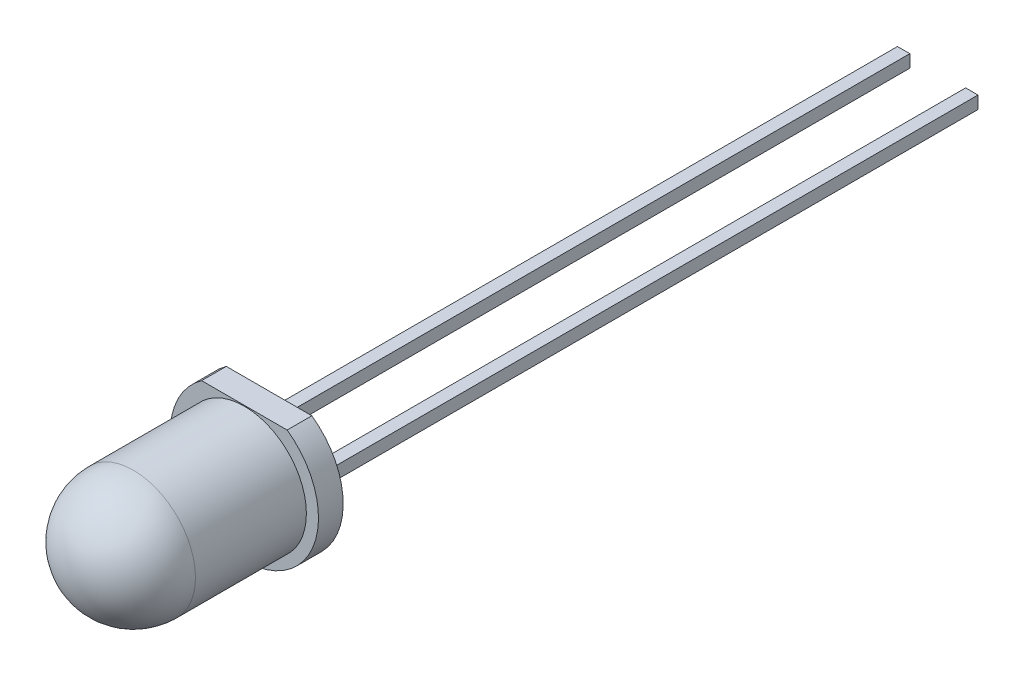
SolidWorks part; units mm, degrees
ref_plane "Front Plane" through (0, 0, 0) normal (0, 0, 1) x (1, 0, 0)
ref_plane "Top Plane" through (0, 0, 0) normal (0, 1, 0) x (1, 0, 0)
ref_plane "Right Plane" through (0, 0, 0) normal (1, 0, 0) x (0, 0, -1)
sketch "Sketch1" plane through (0, 0, 0) normal (0, 0, 1) x (1, 0, 0)
  line L0 (-1.7313, 2.45) -> (1.7313, 2.45)
  line L1 (0, 0) -> (0, -3) construction
  arc A0 (-1.7313, 2.45) -> (1.7313, 2.45) centre (0, 0) ccw
  point P1 (0, -3)
  point P5 (0, 0)
  dimension "D1" = 6
  dimension "D3" = 5.45
extrude "Boss-Extrude2" add sketch "Sketch1" along normal blind 1
sketch "Sketch2" plane through (0, 0, 0) normal (0, 0, -1) x (-1, 0, 0)
  line L0 (0, 0) -> (0, 2.45) construction
  line L1 (-1.7313, 2.45) -> (1.7313, 2.45) construction
  line L2 (0, 2.45) -> (0, -3) construction
  line L4 (-0.25, 1.05) -> (0.25, 1.05)
  line L5 (-0.25, 1.05) -> (-0.25, 1.56)
  line L6 (-0.25, 1.56) -> (0.25, 1.56)
  line L7 (0.25, 1.05) -> (0.25, 1.56)
  line L8 (-0.25, 1.05) -> (0.25, 1.56) construction
  line L9 (-0.25, 1.56) -> (0.25, 1.05) construction
  line L10 (-0.25, -1.78) -> (0.25, -1.78)
  line L11 (-0.25, -1.78) -> (-0.25, -1.27)
  line L12 (-0.25, -1.27) -> (0.25, -1.27)
  line L13 (0.25, -1.78) -> (0.25, -1.27)
  line L14 (-0.25, -1.78) -> (0.25, -1.27) construction
  line L15 (-0.25, -1.27) -> (0.25, -1.78) construction
  arc A0 (-1.7313, 2.45) -> (1.7313, 2.45) centre (0, 0) ccw construction
  point P5 (0, 1.305)
  point P14 (0, -1.525)
  dimension "D1" = 0.51
  dimension "D2" = 0.5
  dimension "D3" = 0.89
  dimension "D4" = 1.22
  dimension "D5" = 0.5
  dimension "D6" = 0.51
extrude "Boss-Extrude3" add sketch "Sketch2" along normal blind 25.69
sketch "Sketch4" plane through (0, 0, -25.69) normal (0, 0, -1) x (-1, 0, 0)
  line L1 (0.25, -1.27) -> (-0.25, -1.27)
  line L2 (0.25, -1.27) -> (0.25, -1.78)
  line L3 (0.25, -1.78) -> (-0.25, -1.78)
  line L4 (-0.25, -1.27) -> (-0.25, -1.78)
extrude "Boss-Extrude4" add sketch "Sketch4" along normal blind 2.76
sketch "Sketch5" plane through (0, 0, 1) normal (0, 0, 1) x (1, 0, 0)
  line L0 (0, 2.45) -> (0, 2.42) construction
  line L1 (1.7313, 2.45) -> (-1.7313, 2.45) construction
  line L2 (0, -2.6) -> (-1.3008, -2.6) construction
  circle A0 centre (0, -0.09) radius 2.51
  dimension "D2" = 0.4
  dimension "D1" = 5.02
  dimension "D3" = 2.6
extrude "Boss-Extrude5" add sketch "Sketch5" along normal blind 7
fillet "Fillet2" radius 2.51 1 edges at (2.51, -0.09, 8)
